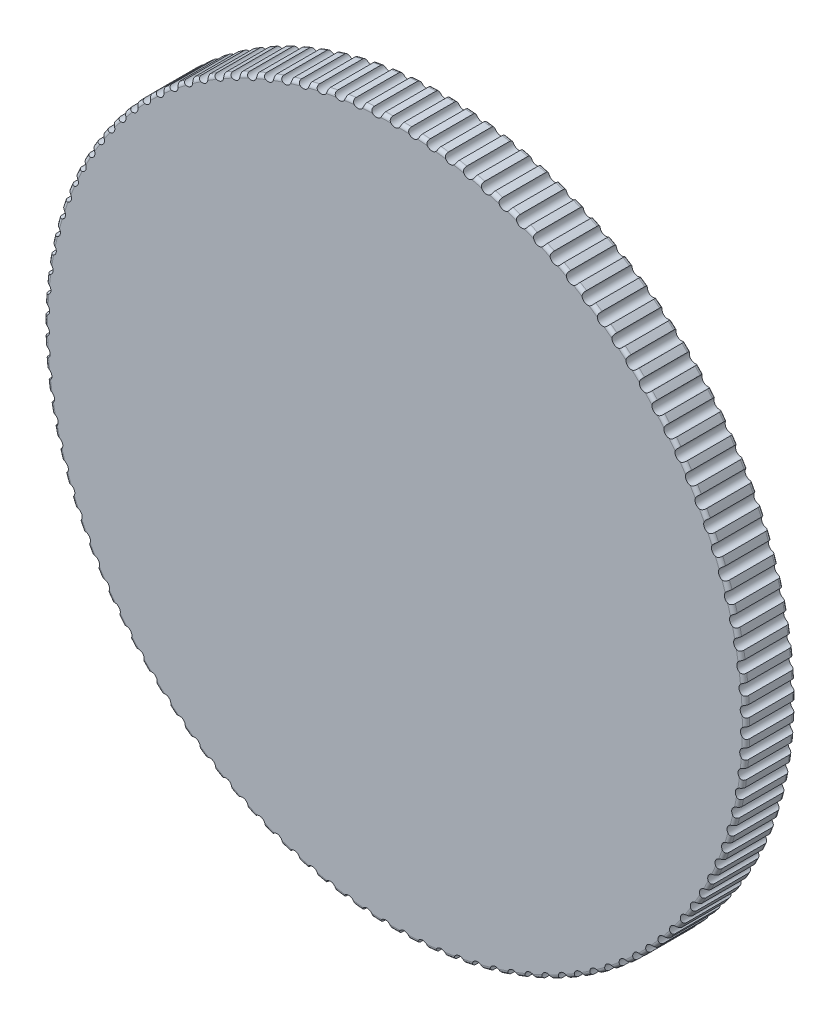
SolidWorks part; units mm, degrees
material "Nickel"
ref_plane "Front Plane" through (0, 0, 0) normal (0, 0, 1) x (1, 0, 0)
ref_plane "Top Plane" through (0, 0, 0) normal (0, 1, 0) x (1, 0, 0)
ref_plane "Right Plane" through (0, 0, 0) normal (1, 0, 0) x (0, 0, -1)
sketch "Sketch1" plane through (0, 0, 0) normal (0, 0, 1) x (1, 0, 0)
  circle A0 centre (0, 0) radius 12.1031
  dimension "D1" = 24.2062
extrude "Extrude1" add sketch "Sketch1" along normal blind 1.7272
fillet "Fillet1" radius 0.127 2 edges at (12.1031, 0, 0) (12.1031, 0, 1.7272)
sketch "Sketch2" plane through (0, 0, 1.7272) normal (0, 0, 1) x (1, 0, 0)
  circle A0 centre (0, 12.1031) radius 0.1905
  circle A1 centre (0, 0) radius 12.1031 construction
  circle A2 centre (0.6387, 12.0862) radius 0.1905
  circle A3 centre (1.2757, 12.0357) radius 0.1905
  circle A4 centre (1.9091, 11.9516) radius 0.1905
  circle A5 centre (2.5372, 11.8342) radius 0.1905
  circle A6 centre (3.1582, 11.6838) radius 0.1905
  circle A7 centre (3.7704, 11.5008) radius 0.1905
  circle A8 centre (4.3721, 11.2858) radius 0.1905
  circle A9 centre (4.9617, 11.0393) radius 0.1905
  circle A10 centre (5.5374, 10.7621) radius 0.1905
  circle A11 centre (6.0976, 10.4549) radius 0.1905
  circle A12 centre (6.6409, 10.1185) radius 0.1905
  circle A13 centre (7.1656, 9.7539) radius 0.1905
  circle A14 centre (7.6704, 9.3622) radius 0.1905
  circle A15 centre (8.1538, 8.9443) radius 0.1905
  circle A16 centre (8.6145, 8.5015) radius 0.1905
  circle A17 centre (9.0511, 8.035) radius 0.1905
  circle A18 centre (9.4626, 7.5462) radius 0.1905
  circle A19 centre (9.8476, 7.0363) radius 0.1905
  circle A20 centre (10.2053, 6.5067) radius 0.1905
  circle A21 centre (10.5344, 5.9591) radius 0.1905
  circle A22 centre (10.8343, 5.3948) radius 0.1905
  circle A23 centre (11.1039, 4.8155) radius 0.1905
  circle A24 centre (11.3425, 4.2228) radius 0.1905
  circle A25 centre (11.5496, 3.6183) radius 0.1905
  circle A26 centre (11.7244, 3.0037) radius 0.1905
  circle A27 centre (11.8666, 2.3808) radius 0.1905
  circle A28 centre (11.9757, 1.7512) radius 0.1905
  circle A29 centre (12.0515, 1.1167) radius 0.1905
  circle A30 centre (12.0936, 0.4792) radius 0.1905
  circle A31 centre (12.102, -0.1598) radius 0.1905
  circle A32 centre (12.0767, -0.7982) radius 0.1905
  circle A33 centre (12.0178, -1.4345) radius 0.1905
  circle A34 centre (11.9253, -2.0667) radius 0.1905
  circle A35 centre (11.7997, -2.6932) radius 0.1905
  circle A36 centre (11.6411, -3.3122) radius 0.1905
  circle A37 centre (11.45, -3.9219) radius 0.1905
  circle A38 centre (11.2271, -4.5207) radius 0.1905
  circle A39 centre (10.9729, -5.1069) radius 0.1905
  circle A40 centre (10.6881, -5.6789) radius 0.1905
  circle A41 centre (10.3735, -6.2351) radius 0.1905
  circle A42 centre (10.03, -6.7739) radius 0.1905
  circle A43 centre (9.6585, -7.2937) radius 0.1905
  circle A44 centre (9.2601, -7.7933) radius 0.1905
  circle A45 centre (8.8359, -8.2712) radius 0.1905
  circle A46 centre (8.3871, -8.7259) radius 0.1905
  circle A47 centre (7.9149, -9.1564) radius 0.1905
  circle A48 centre (7.4206, -9.5614) radius 0.1905
  circle A49 centre (6.9057, -9.9397) radius 0.1905
  circle A50 centre (6.3715, -10.2903) radius 0.1905
  circle A51 centre (5.8195, -10.6122) radius 0.1905
  circle A52 centre (5.2513, -10.9045) radius 0.1905
  circle A53 centre (4.6685, -11.1665) radius 0.1905
  circle A54 centre (4.0727, -11.3973) radius 0.1905
  circle A55 centre (3.4655, -11.5963) radius 0.1905
  circle A56 centre (2.8487, -11.7631) radius 0.1905
  circle A57 centre (2.2239, -11.897) radius 0.1905
  circle A58 centre (1.593, -11.9978) radius 0.1905
  circle A59 centre (0.9576, -12.0652) radius 0.1905
  circle A60 centre (0.3195, -12.0989) radius 0.1905
  circle A61 centre (-0.3195, -12.0989) radius 0.1905
  circle A62 centre (-0.9576, -12.0652) radius 0.1905
  circle A63 centre (-1.593, -11.9978) radius 0.1905
  circle A64 centre (-2.2239, -11.897) radius 0.1905
  circle A65 centre (-2.8487, -11.7631) radius 0.1905
  circle A66 centre (-3.4655, -11.5963) radius 0.1905
  circle A67 centre (-4.0727, -11.3973) radius 0.1905
  circle A68 centre (-4.6685, -11.1665) radius 0.1905
  circle A69 centre (-5.2513, -10.9045) radius 0.1905
  circle A70 centre (-5.8195, -10.6122) radius 0.1905
  circle A71 centre (-6.3715, -10.2903) radius 0.1905
  circle A72 centre (-6.9057, -9.9397) radius 0.1905
  circle A73 centre (-7.4206, -9.5614) radius 0.1905
  circle A74 centre (-7.9149, -9.1564) radius 0.1905
  circle A75 centre (-8.3871, -8.7259) radius 0.1905
  circle A76 centre (-8.8359, -8.2712) radius 0.1905
  circle A77 centre (-9.2601, -7.7933) radius 0.1905
  circle A78 centre (-9.6585, -7.2937) radius 0.1905
  circle A79 centre (-10.03, -6.7739) radius 0.1905
  circle A80 centre (-10.3735, -6.2351) radius 0.1905
  circle A81 centre (-10.6881, -5.6789) radius 0.1905
  circle A82 centre (-10.9729, -5.1069) radius 0.1905
  circle A83 centre (-11.2271, -4.5207) radius 0.1905
  circle A84 centre (-11.45, -3.9219) radius 0.1905
  circle A85 centre (-11.6411, -3.3122) radius 0.1905
  circle A86 centre (-11.7997, -2.6932) radius 0.1905
  circle A87 centre (-11.9253, -2.0667) radius 0.1905
  circle A88 centre (-12.0178, -1.4345) radius 0.1905
  circle A89 centre (-12.0767, -0.7982) radius 0.1905
  circle A90 centre (-12.102, -0.1598) radius 0.1905
  circle A91 centre (-12.0936, 0.4792) radius 0.1905
  circle A92 centre (-12.0515, 1.1167) radius 0.1905
  circle A93 centre (-11.9757, 1.7512) radius 0.1905
  circle A94 centre (-11.8666, 2.3808) radius 0.1905
  circle A95 centre (-11.7244, 3.0037) radius 0.1905
  circle A96 centre (-11.5496, 3.6183) radius 0.1905
  circle A97 centre (-11.3425, 4.2228) radius 0.1905
  circle A98 centre (-11.1039, 4.8155) radius 0.1905
  circle A99 centre (-10.8343, 5.3948) radius 0.1905
  circle A100 centre (-10.5344, 5.9591) radius 0.1905
  circle A101 centre (-10.2053, 6.5067) radius 0.1905
  circle A102 centre (-9.8476, 7.0363) radius 0.1905
  circle A103 centre (-9.4626, 7.5462) radius 0.1905
  circle A104 centre (-9.0511, 8.035) radius 0.1905
  circle A105 centre (-8.6145, 8.5015) radius 0.1905
  circle A106 centre (-8.1538, 8.9443) radius 0.1905
  circle A107 centre (-7.6704, 9.3622) radius 0.1905
  circle A108 centre (-7.1656, 9.7539) radius 0.1905
  circle A109 centre (-6.6409, 10.1185) radius 0.1905
  circle A110 centre (-6.0976, 10.4549) radius 0.1905
  circle A111 centre (-5.5374, 10.7621) radius 0.1905
  circle A112 centre (-4.9617, 11.0393) radius 0.1905
  circle A113 centre (-4.3721, 11.2858) radius 0.1905
  circle A114 centre (-3.7704, 11.5008) radius 0.1905
  circle A115 centre (-3.1582, 11.6838) radius 0.1905
  circle A116 centre (-2.5372, 11.8342) radius 0.1905
  circle A117 centre (-1.9091, 11.9516) radius 0.1905
  circle A118 centre (-1.2757, 12.0357) radius 0.1905
  circle A119 centre (-0.6387, 12.0862) radius 0.1905
  dimension "D1" = 0.381
extrude "Cut-Extrude1" cut sketch "Sketch2" against normal through all
